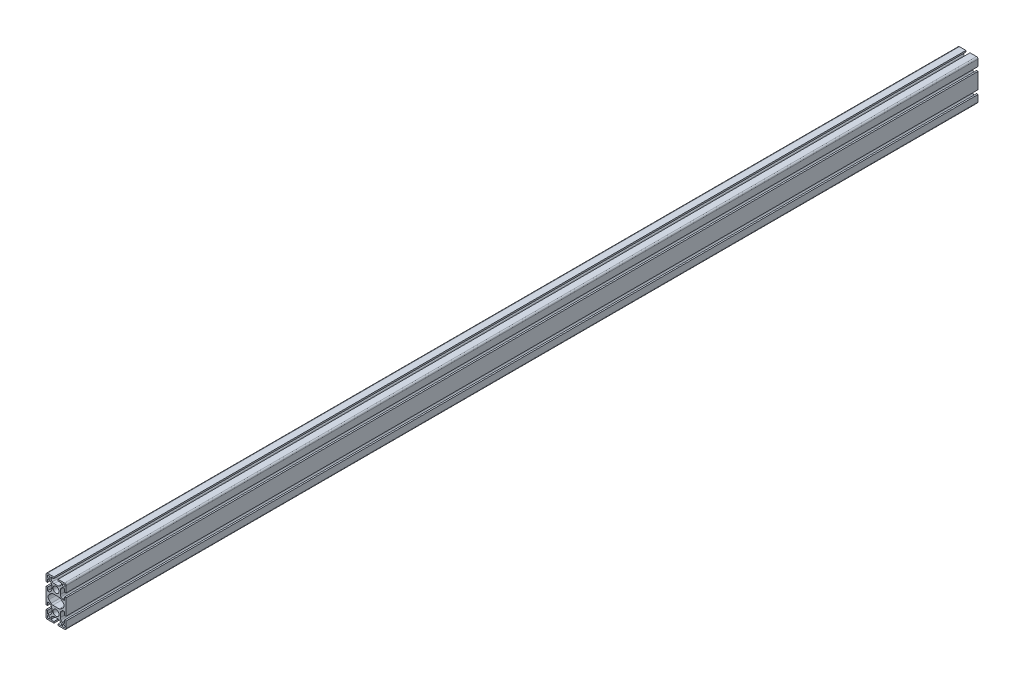
SolidWorks part; units mm, degrees
ref_plane "Front Plane" through (0, 0, 0) normal (0, 0, 1) x (1, 0, 0)
ref_plane "Top Plane" through (0, 0, 0) normal (0, 1, 0) x (1, 0, 0)
ref_plane "Right Plane" through (0, 0, 0) normal (1, 0, 0) x (0, 0, -1)
sketch "Sketch1" plane through (0, 0, 0) normal (0, 0, 1) x (1, 0, 0)
  line L0 (-17, -40) -> (-4.1, -40)
  line L1 (-4.1, -40) -> (-4.1, -37)
  line L2 (-4.1, -37) -> (-10.5, -37)
  line L3 (-10.5, -37) -> (-10.5, -33.6627)
  line L4 (-10.0314, -32.5314) -> (-7.4645, -29.9645)
  line L5 (-3.9289, -28.5) -> (3.9289, -28.5)
  line L6 (7.4645, -29.9645) -> (10.0314, -32.5314)
  line L7 (10.5, -33.6627) -> (10.5, -37)
  line L8 (10.5, -37) -> (4.1, -37)
  line L9 (4.1, -37) -> (4.1, -40)
  line L10 (4.1, -40) -> (17, -40)
  line L11 (20, -37) -> (20, -24.1)
  line L12 (20, -24.1) -> (17, -24.1)
  line L13 (17, -24.1) -> (17, -30.5)
  line L14 (17, -30.5) -> (13.6627, -30.5)
  line L15 (12.5314, -30.0314) -> (9.9645, -27.4645)
  line L16 (8.5, -23.9289) -> (8.5, -16.0711)
  line L17 (9.9645, -12.5355) -> (12.5314, -9.9686)
  line L18 (13.6627, -9.5) -> (17, -9.5)
  line L19 (17, -9.5) -> (17, -15.9)
  line L20 (17, -15.9) -> (20, -15.9)
  line L21 (20, -15.9) -> (20, 15.9)
  line L22 (20, 15.9) -> (17, 15.9)
  line L23 (17, 15.9) -> (17, 9.5)
  line L24 (17, 9.5) -> (13.6627, 9.5)
  line L25 (12.5314, 9.9686) -> (9.9645, 12.5355)
  line L26 (8.5, 16.0711) -> (8.5, 23.9289)
  line L27 (9.9645, 27.4645) -> (12.5314, 30.0314)
  line L28 (13.6627, 30.5) -> (17, 30.5)
  line L29 (17, 30.5) -> (17, 24.1)
  line L30 (17, 24.1) -> (20, 24.1)
  line L31 (20, 24.1) -> (20, 37)
  line L32 (17, 40) -> (4.1, 40)
  line L33 (4.1, 40) -> (4.1, 37)
  line L34 (4.1, 37) -> (10.5, 37)
  line L35 (10.5, 37) -> (10.5, 33.6627)
  line L36 (10.0314, 32.5314) -> (7.4645, 29.9645)
  line L37 (3.9289, 28.5) -> (-3.9289, 28.5)
  line L38 (-7.4645, 29.9645) -> (-10.0314, 32.5314)
  line L39 (-10.5, 33.6627) -> (-10.5, 37)
  line L40 (-10.5, 37) -> (-4.1, 37)
  line L41 (-4.1, 37) -> (-4.1, 40)
  line L42 (-4.1, 40) -> (-17, 40)
  line L43 (-20, 37) -> (-20, 24.1)
  line L44 (-20, 24.1) -> (-17, 24.1)
  line L45 (-17, 24.1) -> (-17, 30.5)
  line L46 (-17, 30.5) -> (-13.6627, 30.5)
  line L47 (-12.5314, 30.0314) -> (-9.9645, 27.4645)
  line L48 (-8.5, 23.9289) -> (-8.5, 16.0711)
  line L49 (-9.9645, 12.5355) -> (-12.5314, 9.9686)
  line L50 (-13.6627, 9.5) -> (-17, 9.5)
  line L51 (-17, 9.5) -> (-17, 15.9)
  line L52 (-17, 15.9) -> (-20, 15.9)
  line L53 (-20, 15.9) -> (-20, -15.9)
  line L54 (-20, -15.9) -> (-17, -15.9)
  line L55 (-17, -15.9) -> (-17, -9.5)
  line L56 (-17, -9.5) -> (-13.6627, -9.5)
  line L57 (-12.5314, -9.9686) -> (-9.9645, -12.5355)
  line L58 (-8.5, -16.0711) -> (-8.5, -23.9289)
  line L59 (-9.9645, -27.4645) -> (-12.5314, -30.0314)
  line L60 (-13.6627, -30.5) -> (-17, -30.5)
  line L61 (-17, -30.5) -> (-17, -24.1)
  line L62 (-17, -24.1) -> (-20, -24.1)
  line L63 (-20, -24.1) -> (-20, -37)
  line L64 (-14.2426, -4.2426) -> (-9.9497, -8.5355)
  line L65 (-6.4142, -10) -> (6.4142, -10)
  line L66 (9.9497, -8.5355) -> (14.2426, -4.2426)
  line L67 (14.2426, 4.2426) -> (9.9497, 8.5355)
  line L68 (6.4142, 10) -> (-6.4142, 10)
  line L69 (-9.9497, 8.5355) -> (-14.2426, 4.2426)
  arc A0 (-20, -37) -> (-17, -40) centre (-17, -37) ccw
  arc A1 (-10.5, -33.6627) -> (-10.0314, -32.5314) centre (-8.9, -33.6627) cw
  arc A2 (-7.4645, -29.9645) -> (-3.9289, -28.5) centre (-3.9289, -33.5) cw
  arc A3 (3.9289, -28.5) -> (7.4645, -29.9645) centre (3.9289, -33.5) cw
  arc A4 (10.0314, -32.5314) -> (10.5, -33.6627) centre (8.9, -33.6627) cw
  arc A5 (17, -40) -> (20, -37) centre (17, -37) ccw
  arc A6 (13.6627, -30.5) -> (12.5314, -30.0314) centre (13.6627, -28.9) cw
  arc A7 (9.9645, -27.4645) -> (8.5, -23.9289) centre (13.5, -23.9289) cw
  arc A8 (8.5, -16.0711) -> (9.9645, -12.5355) centre (13.5, -16.0711) cw
  arc A9 (12.5314, -9.9686) -> (13.6627, -9.5) centre (13.6627, -11.1) cw
  arc A10 (13.6627, 9.5) -> (12.5314, 9.9686) centre (13.6627, 11.1) cw
  arc A11 (9.9645, 12.5355) -> (8.5, 16.0711) centre (13.5, 16.0711) cw
  arc A12 (8.5, 23.9289) -> (9.9645, 27.4645) centre (13.5, 23.9289) cw
  arc A13 (12.5314, 30.0314) -> (13.6627, 30.5) centre (13.6627, 28.9) cw
  arc A14 (20, 37) -> (17, 40) centre (17, 37) ccw
  arc A15 (10.5, 33.6627) -> (10.0314, 32.5314) centre (8.9, 33.6627) cw
  arc A16 (7.4645, 29.9645) -> (3.9289, 28.5) centre (3.9289, 33.5) cw
  arc A17 (-3.9289, 28.5) -> (-7.4645, 29.9645) centre (-3.9289, 33.5) cw
  arc A18 (-10.0314, 32.5314) -> (-10.5, 33.6627) centre (-8.9, 33.6627) cw
  arc A19 (-17, 40) -> (-20, 37) centre (-17, 37) ccw
  arc A20 (-13.6627, 30.5) -> (-12.5314, 30.0314) centre (-13.6627, 28.9) cw
  arc A21 (-9.9645, 27.4645) -> (-8.5, 23.9289) centre (-13.5, 23.9289) cw
  arc A22 (-8.5, 16.0711) -> (-9.9645, 12.5355) centre (-13.5, 16.0711) cw
  arc A23 (-12.5314, 9.9686) -> (-13.6627, 9.5) centre (-13.6627, 11.1) cw
  arc A24 (-13.6627, -9.5) -> (-12.5314, -9.9686) centre (-13.6627, -11.1) cw
  arc A25 (-9.9645, -12.5355) -> (-8.5, -16.0711) centre (-13.5, -16.0711) cw
  arc A26 (-8.5, -23.9289) -> (-9.9645, -27.4645) centre (-13.5, -23.9289) cw
  arc A27 (-12.5314, -30.0314) -> (-13.6627, -30.5) centre (-13.6627, -28.9) cw
  circle A28 centre (15, 35) radius 2.5
  circle A29 centre (15, -35) radius 2.5
  circle A30 centre (0, 20) radius 6
  circle A31 centre (0, -20) radius 6
  arc A32 (-14.2426, 4.2426) -> (-14.2426, -4.2426) centre (-10, 0) ccw
  arc A33 (-9.9497, -8.5355) -> (-6.4142, -10) centre (-6.4142, -5) ccw
  arc A34 (6.4142, -10) -> (9.9497, -8.5355) centre (6.4142, -5) ccw
  arc A35 (14.2426, -4.2426) -> (14.2426, 4.2426) centre (10, 0) ccw
  arc A36 (9.9497, 8.5355) -> (6.4142, 10) centre (6.4142, 5) ccw
  arc A37 (-6.4142, 10) -> (-9.9497, 8.5355) centre (-6.4142, 5) ccw
  circle A38 centre (-15, 35) radius 2.5
  circle A39 centre (-15, -35) radius 2.5
  dimension "D1" = 40
  dimension "D2" = 80
extrude "Boss-Extrude1" add sketch "Sketch1" against normal blind 1820
